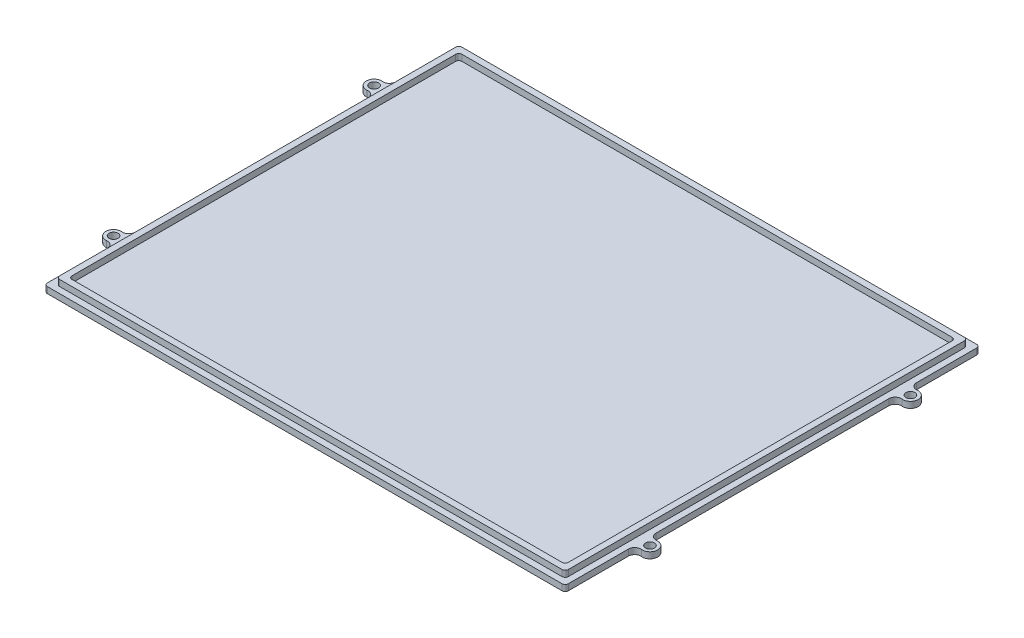
SolidWorks part; units mm, degrees
ref_plane "前视基准面" through (0, 0, 0) normal (0, 0, 1) x (1, 0, 0)
ref_plane "上视基准面" through (0, 0, 0) normal (0, 1, 0) x (1, 0, 0)
ref_plane "右视基准面" through (0, 0, 0) normal (1, 0, 0) x (0, 0, -1)
sketch "草图1" plane through (0, 0, 0) normal (0, 1, 0) x (1, 0, 0)
  line L1 (-83.5, -67.25) -> (83.5, -67.25)
  line L2 (-84.5, -66.25) -> (-84.5, 66.25)
  line L3 (-83.5, 67.25) -> (83.5, 67.25)
  line L4 (84.5, -66.25) -> (84.5, 66.25)
  line L5 (-84.5, -67.25) -> (84.5, 67.25) construction
  line L6 (-84.5, 67.25) -> (84.5, -67.25) construction
  arc A0 (-83.5, -67.25) -> (-84.5, -66.25) centre (-83.5, -66.25) cw
  arc A1 (83.5, -67.25) -> (84.5, -66.25) centre (83.5, -66.25) ccw
  arc A2 (83.5, 67.25) -> (84.5, 66.25) centre (83.5, 66.25) cw
  arc A3 (-84.5, 66.25) -> (-83.5, 67.25) centre (-83.5, 66.25) cw
  point P0 (0, 0)
  dimension "D3" = 1
  dimension "D1" = 169
  dimension "D2" = 134.5
extrude "凸台-拉伸1" add sketch "草图1" along normal blind 2
sketch "草图2" plane through (0, 2, 0) normal (0, 1, 0) x (1, 0, 0)
  line L0 (79.5, 63.25) -> (-79.5, 63.25)
  line L1 (-80.5, 62.25) -> (-80.5, -62.25)
  line L2 (80.5, -62.25) -> (80.5, 62.25)
  line L3 (-79.5, -63.25) -> (79.5, -63.25)
  line L5 (80.5, -64.25) -> (80.5, 64.25) construction
  line L6 (81.5, 63.25) -> (-80.5, 63.25) construction
  line L7 (-81.5, -63.25) -> (81.5, -63.25) construction
  line L8 (-82.5, -65.25) -> (82.5, -65.25)
  line L9 (82.5, -65.25) -> (82.5, 65.25)
  line L10 (82.5, 65.25) -> (-82.5, 65.25)
  line L11 (-82.5, 65.25) -> (-82.5, -65.25)
  line L12 (-81.5, -65.25) -> (81.5, -65.25)
  line L13 (82.5, -64.25) -> (82.5, 64.25)
  line L14 (81.5, 65.25) -> (-81.5, 65.25)
  line L15 (-82.5, 64.25) -> (-82.5, -64.25)
  line L16 (-80.5, 63.25) -> (-80.5, -64.25) construction
  arc A1 (-80.5, -62.25) -> (-79.5, -63.25) centre (-79.5, -62.25) ccw
  arc A2 (79.5, -63.25) -> (80.5, -62.25) centre (79.5, -62.25) ccw
  arc A3 (79.5, 63.25) -> (80.5, 62.25) centre (79.5, 62.25) cw
  arc A4 (-81.5, -65.25) -> (-82.5, -64.25) centre (-81.5, -64.25) cw
  arc A5 (81.5, -65.25) -> (82.5, -64.25) centre (81.5, -64.25) ccw
  arc A6 (82.5, 64.25) -> (81.5, 65.25) centre (81.5, 64.25) ccw
  arc A7 (-81.5, 65.25) -> (-82.5, 64.25) centre (-81.5, 64.25) ccw
  arc A8 (-79.5, 63.25) -> (-80.5, 62.25) centre (-79.5, 62.25) ccw
  arc A9 (-80.5, 63.25) -> (-80.5, 63.25) centre (-80.5, 63.25) ccw construction
  dimension "D2" = 1
  dimension "D4" = 1
  dimension "D1" = 2
  dimension "D3" = 2
extrude "凸台-拉伸2" add sketch "草图2" along normal blind 2
sketch "草图3" plane through (0, 0, 0) normal (0, -1, 0) x (1, 0, 0)
  line L0 (-84.5, -66.25) -> (-84.5, 66.25) construction
  line L1 (-83.5, 67.25) -> (83.5, 67.25) construction
  line L2 (-84.5, 37.7779) -> (-86.7222, 39.7655) construction
  line L3 (-86.7222, 44.7345) -> (-84.5, 46.7221) construction
  line L4 (-84.5, 46.7221) -> (-84.5, 37.7779)
  line L5 (0, 106.9566) -> (0, -99.3581) construction
  line L6 (86.7222, 44.7345) -> (84.5, 46.7221) construction
  line L7 (84.5, 37.7779) -> (86.7222, 39.7655) construction
  line L8 (84.5, 46.7221) -> (84.5, 37.7779)
  line L9 (-33.9409, 0) -> (31.0412, 0) construction
  line L10 (84.5, -37.7779) -> (86.7222, -39.7655) construction
  line L11 (86.7222, -44.7345) -> (84.5, -46.7221) construction
  line L12 (-86.7222, -44.7345) -> (-84.5, -46.7221) construction
  line L13 (-84.5, -37.7779) -> (-86.7222, -39.7655) construction
  line L14 (84.5, -46.7221) -> (84.5, -37.7779)
  line L15 (-84.5, -46.7221) -> (-84.5, -37.7779)
  arc A0 (-86.7222, 44.7345) -> (-86.7222, 39.7655) centre (-87, 42.25) ccw
  arc A1 (-86.7222, 44.7345) -> (-84.5, 46.7221) centre (-86.5, 46.7221) ccw
  arc A2 (-84.5, 37.7779) -> (-86.7222, 39.7655) centre (-86.5, 37.7779) ccw
  circle A3 centre (-87, 42.25) radius 1.45
  circle A4 centre (87, 42.25) radius 1.45
  arc A5 (84.5, 37.7779) -> (86.7222, 39.7655) centre (86.5, 37.7779) cw
  arc A6 (86.7222, 44.7345) -> (84.5, 46.7221) centre (86.5, 46.7221) cw
  arc A7 (86.7222, 44.7345) -> (86.7222, 39.7655) centre (87, 42.25) cw
  arc A8 (86.7222, -44.7345) -> (86.7222, -39.7655) centre (87, -42.25) ccw
  arc A9 (86.7222, -44.7345) -> (84.5, -46.7221) centre (86.5, -46.7221) ccw
  arc A10 (84.5, -37.7779) -> (86.7222, -39.7655) centre (86.5, -37.7779) ccw
  circle A11 centre (87, -42.25) radius 1.45
  circle A12 centre (-87, -42.25) radius 1.45
  arc A13 (-84.5, -37.7779) -> (-86.7222, -39.7655) centre (-86.5, -37.7779) cw
  arc A14 (-86.7222, -44.7345) -> (-84.5, -46.7221) centre (-86.5, -46.7221) cw
  arc A15 (-86.7222, -44.7345) -> (-86.7222, -39.7655) centre (-87, -42.25) cw
  point P41 (0, 0)
  dimension "D1" = 5
  dimension "D2" = 25
  dimension "D3" = 4
  dimension "D4" = 4
  dimension "D5" = 2.9
sketch "草图5" plane through (0, 0, 0) normal (0, -1, 0) x (1, 0, 0)
extrude "凸台-拉伸5" add sketch "草图3" against normal blind 2
